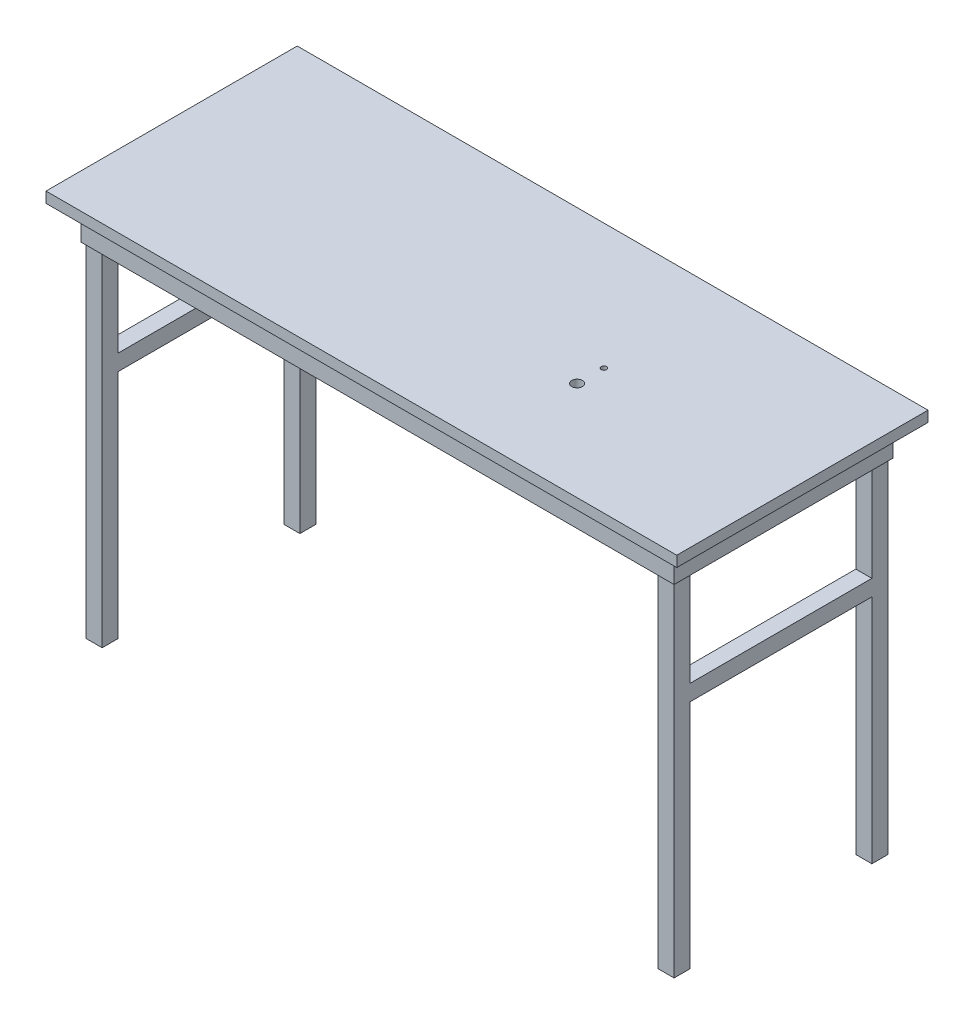
SolidWorks part; units mm, degrees
material "Pine"
ref_plane "Front Plane" through (0, 0, 0) normal (0, 0, 1) x (1, 0, 0)
ref_plane "Top Plane" through (0, 0, 0) normal (0, 1, 0) x (1, 0, 0)
ref_plane "Right Plane" through (0, 0, 0) normal (1, 0, 0) x (0, 0, -1)
sketch "Sketch1" plane through (0, 0, 0) normal (0, 1, 0) x (1, 0, 0)
  line L1 (749.3, -298.45) -> (-749.3, -298.45)
  line L2 (749.3, -298.45) -> (749.3, 298.45)
  line L3 (749.3, 298.45) -> (-749.3, 298.45)
  line L4 (-749.3, -298.45) -> (-749.3, 298.45)
  line L5 (749.3, -298.45) -> (-749.3, 298.45) construction
  line L6 (749.3, 298.45) -> (-749.3, -298.45) construction
  point P0 (0, 0)
  dimension "D1" = 1498.6
  dimension "D2" = 596.9
extrude "Boss-Extrude1" add sketch "Sketch1" along normal blind 25.4
sketch "Sketch3" plane through (0, 25.4, 0) normal (0, -1, 0) x (1, 0, 0)
  line L0 (0, -13.97) -> (0, 13.97) construction
  line L1 (-698.5, 254) -> (-660.4, 254)
  line L2 (-698.5, 254) -> (-698.5, 215.9)
  line L3 (-698.5, 215.9) -> (-660.4, 215.9)
  line L4 (-660.4, 254) -> (-660.4, 215.9)
  line L5 (698.5, 254) -> (698.5, 215.9)
  line L6 (698.5, 215.9) -> (660.4, 215.9)
  line L7 (660.4, 254) -> (660.4, 215.9)
  line L8 (698.5, 254) -> (660.4, 254)
  line L9 (13.97, 0) -> (-13.97, 0) construction
  line L10 (698.5, -254) -> (660.4, -254)
  line L11 (660.4, -254) -> (660.4, -215.9)
  line L12 (698.5, -215.9) -> (660.4, -215.9)
  line L13 (698.5, -254) -> (698.5, -215.9)
  line L14 (-660.4, -254) -> (-660.4, -215.9)
  line L15 (-698.5, -215.9) -> (-660.4, -215.9)
  line L16 (-698.5, -254) -> (-698.5, -215.9)
  line L17 (-698.5, -254) -> (-660.4, -254)
  dimension "D1" = 1397
  dimension "D2" = 508
  dimension "D4" = 38.1
extrude "Boss-Extrude2" add sketch "Sketch3" along normal blind 917.575
sketch "Sketch4" plane through (698.5, 0, 0) normal (1, 0, 0) x (0, 0, -1)
  line L1 (-254, -892.175) -> (-254, 0) construction
  line L2 (-254, -304.8) -> (254, -304.8)
  line L3 (-254, -304.8) -> (-254, -342.9)
  line L4 (-254, -342.9) -> (254, -342.9)
  line L5 (254, -304.8) -> (254, -342.9)
  line L6 (254, -892.175) -> (254, 0) construction
  line L7 (-215.9, -892.175) -> (-254, -892.175) construction
  line L8 (-298.45, 0) -> (298.45, 0) construction
  dimension "D1" = 304.8
extrude "Boss-Extrude3" add sketch "Sketch4" along direction (1, 0, 0) on the side against the normal blind 38.1
mirror "Mirror1" about plane through (0, 0, 0) normal (1, 0, 0) of "Boss-Extrude3"
hole_wizard "1/2 (0.5) Diameter Hole1" positions "Sketch7" profile "Sketch8" hole size "1/2" standard "ANSI Inch" end condition through all
sketch "Sketch7" plane through (0, 25.4, 0) normal (0, 1, 0) x (1, 0, 0)
  point P0 (277.7125, 0)
  point P4 (276.4559, -26.389)
  point P5 (0, 0)
  dimension "D1" = 277.7125
sketch "Sketch8" plane through (277.7125, 25.4, 0) normal (1, 0, 0) x (0, 0, 1)
  line L0 (0, 0) -> (0, 917.575)
  line L1 (0, 917.575) -> (6.35, 917.575)
  line L2 (6.35, 917.575) -> (6.35, 0)
  line L5 (6.35, 0) -> (0, 0)
  line L11 (0, -6.35) -> (0, 107.95) construction
  dimension "Thru Hole Dia." = 12.7
  dimension "Thru Hole Depth" = 917.575
sketch "Sketch9" plane through (0, 0, 0) normal (0, -1, 0) x (1, 0, 0)
  line L1 (-704.85, -260.35) -> (704.85, -260.35)
  line L2 (-704.85, -260.35) -> (-704.85, 260.35)
  line L3 (-704.85, 260.35) -> (704.85, 260.35)
  line L4 (704.85, -260.35) -> (704.85, 260.35)
  line L5 (-704.85, -260.35) -> (704.85, 260.35) construction
  line L6 (-704.85, 260.35) -> (704.85, -260.35) construction
  line L7 (698.5, -254) -> (-698.5, -254)
  line L8 (698.5, -254) -> (698.5, 254)
  line L9 (698.5, 254) -> (-698.5, 254)
  line L10 (-698.5, -254) -> (-698.5, 254)
  line L11 (698.5, -254) -> (-698.5, 254) construction
  line L12 (698.5, 254) -> (-698.5, -254) construction
  point P0 (0, 0)
  point P6 (0, 0)
  point P11 (0, 0)
  dimension "D1" = 6.35
  dimension "D2" = 6.35
extrude "Boss-Extrude4" add sketch "Sketch9" along normal blind 76.2
hole_wizard "1 (1) Diameter Hole3" positions "Sketch10" profile "Sketch11" hole size "1" standard "ANSI Inch" end condition through all
sketch "Sketch10" plane through (0, 25.4, 0) normal (0, 1, 0) x (1, 0, 0)
  circle A0 centre (277.7125, 0) radius 6.35 construction
  circle A1 centre (277.7125, 0) radius 6.35
  point P0 (277.7125, -63.5)
  point P5 (271.6383, -63.5)
  point P7 (0, 0)
  dimension "D1" = 63.5
sketch "Sketch11" plane through (277.7125, 25.4, 63.5) normal (1, 0, 0) x (0, 0, 1)
  line L0 (0, 0) -> (0, 917.575)
  line L1 (0, 917.575) -> (12.7, 917.575)
  line L2 (12.7, 917.575) -> (12.7, 0)
  line L5 (12.7, 0) -> (0, 0)
  line L11 (0, -6.35) -> (0, 107.95) construction
  dimension "Thru Hole Dia." = 25.4
  dimension "Thru Hole Depth" = 917.575
equation "\"D2@Sketch9\"=\"D1@Sketch9\""
